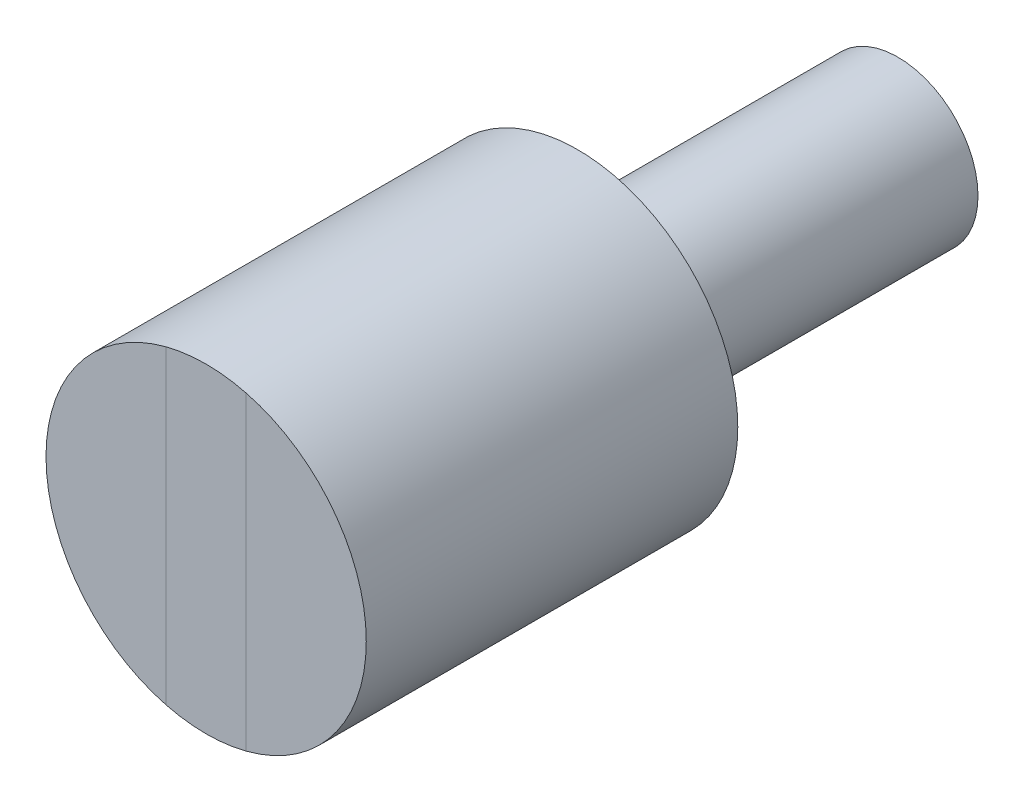
SolidWorks part; units mm, degrees
ref_plane "Front Plane" through (0, 0, 0) normal (0, 0, 1) x (1, 0, 0)
ref_plane "Top Plane" through (0, 0, 0) normal (0, 1, 0) x (1, 0, 0)
ref_plane "Right Plane" through (0, 0, 0) normal (1, 0, 0) x (0, 0, -1)
sketch "sketch1_link6" plane through (0, 0, 0) normal (0, 0, 1) x (1, 0, 0)
  circle A0 centre (0, 0) radius 15
  dimension "D1" = 30
extrude "Boss-Extrude1" add sketch "sketch1_link6" along normal mid plane 60
sketch "sketch2_link6" plane through (0, 0, 30) normal (0, 0, 1) x (1, 0, 0)
  circle A0 centre (0, 0) radius 30
  dimension "D1" = 60
extrude "Boss-Extrude2" add sketch "sketch2_link6" along normal blind 69.6
sketch "sketch3_link6" plane through (0, 0, 99.6) normal (0, 0, 1) x (1, 0, 0)
  line L0 (-7.5, 29.0474) -> (-7.5, -29.0474)
  line L1 (7.5, 29.0474) -> (7.5, -29.0474)
  circle A0 centre (0, 0) radius 30 construction
  arc A1 (7.5, 29.0474) -> (-7.5, 29.0474) centre (0, 0) ccw
  arc A2 (7.5, -29.0474) -> (-7.5, -29.0474) centre (0, 0) cw
  dimension "D1" = 15
extrude "Boss-Extrude3" add sketch "sketch3_link6" along normal blind 0.001
